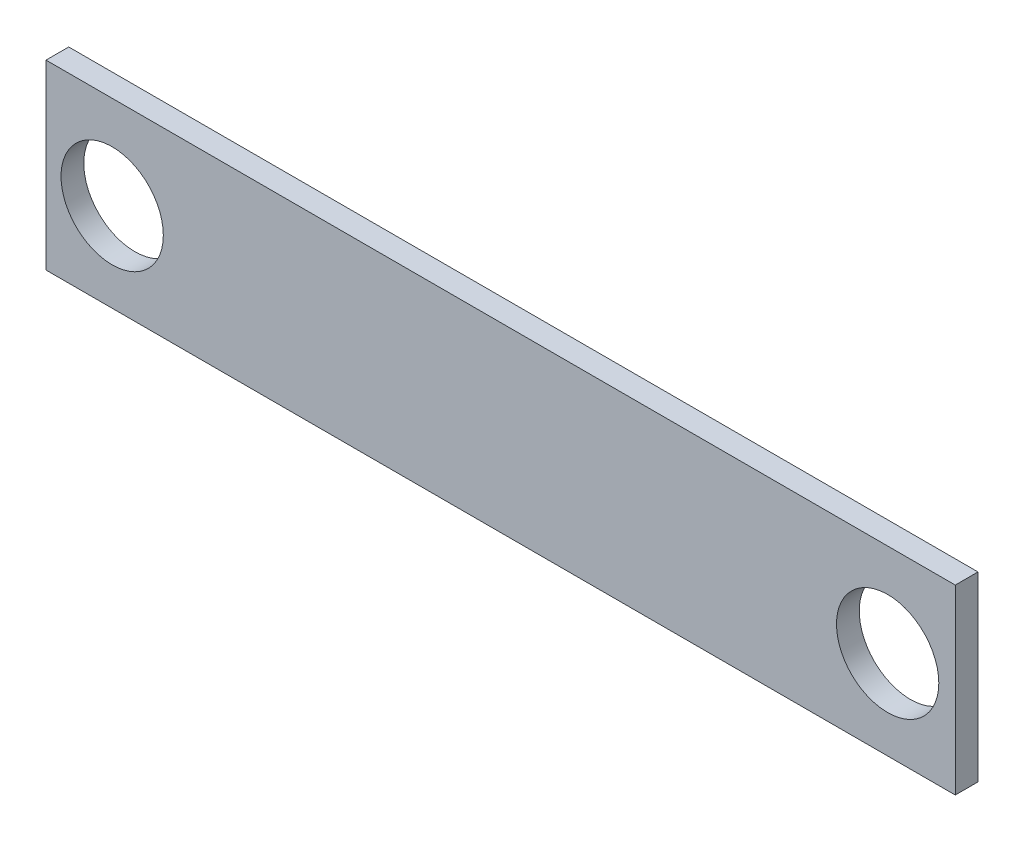
SolidWorks part; units mm, degrees
ref_plane "Front Plane" through (0, 0, 0) normal (0, 0, 1) x (1, 0, 0)
ref_plane "Top Plane" through (0, 0, 0) normal (0, 1, 0) x (1, 0, 0)
ref_plane "Right Plane" through (0, 0, 0) normal (1, 0, 0) x (0, 0, -1)
sketch "Sketch1" plane through (0, 0, 0) normal (0, 0, 1) x (1, 0, 0)
  line L1 (-130.6849, 49.6319) -> (123.3151, 49.6319)
  line L2 (-130.6849, 49.6319) -> (-130.6849, -1.1681)
  line L3 (-130.6849, -1.1681) -> (123.3151, -1.1681)
  line L4 (123.3151, 49.6319) -> (123.3151, -1.1681)
  dimension "D1" = 254
  dimension "D2" = 50.8
extrude "Boss-Extrude1" add sketch "Sketch1" along normal blind 6.35
sketch "Sketch3" plane through (0, 0, 6.35) normal (0, 0, 1) x (1, 0, 0)
  circle A0 centre (-112.2021, 23.6244) radius 14.2875
  circle A1 centre (104.427, 23.6244) radius 14.2875
  dimension "D1" = 28.575
  dimension "D2" = 28.575
extrude "Cut-Extrude1" cut sketch "Sketch3" against normal blind 6.35
